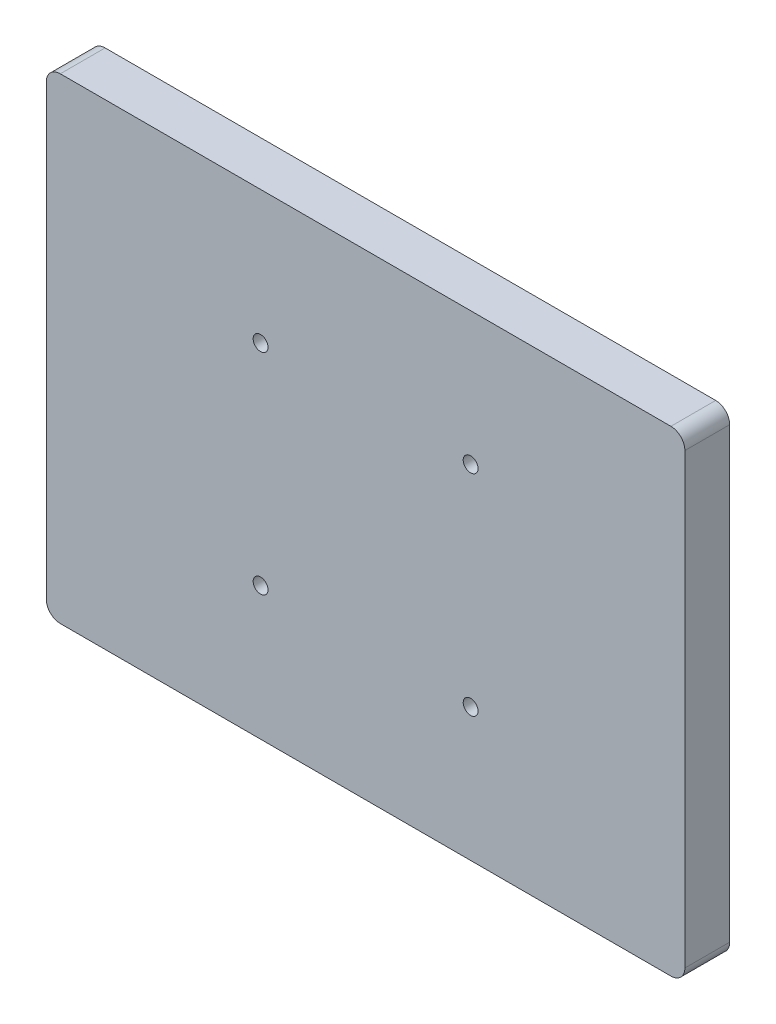
SolidWorks part; units mm, degrees
ref_plane "前视基准面" through (0, 0, 0) normal (0, 0, 1) x (1, 0, 0)
ref_plane "上视基准面" through (0, 0, 0) normal (0, 1, 0) x (1, 0, 0)
ref_plane "右视基准面" through (0, 0, 0) normal (1, 0, 0) x (0, 0, -1)
other "Configuration Table"
sketch "Sketch1" plane through (0, 0, 0) normal (0, 0, 1) x (1, 0, 0)
  line L1 (0, 0) -> (228, 0)
  line L2 (0, 0) -> (0, 170)
  line L3 (0, 170) -> (228, 170)
  line L4 (228, 0) -> (228, 170)
  dimension "D1" = 170
  dimension "D2" = 228
extrude "Boss-Extrude1" add sketch "Sketch1" along normal blind 16
fillet "Fillet1" radius 5 4 edges at (228, 0, 8) (0, 0, 8) (228, 170, 8) (0, 170, 8)
sketch "Sketch2" plane through (0, 0, 16) normal (0, 0, 1) x (1, 0, 0)
  line L0 (0, 85) -> (228, 85) construction
  line L1 (0, 165) -> (0, 5) construction
  line L2 (228, 5) -> (228, 165) construction
  line L3 (114, 170) -> (114, 0) construction
  line L4 (223, 170) -> (5, 170) construction
  line L5 (5, 0) -> (223, 0) construction
  circle A0 centre (76.5, 122.5) radius 2.65
  circle A1 centre (151.5, 122.5) radius 2.65
  circle A2 centre (76.5, 47.5) radius 2.65
  circle A3 centre (151.5, 47.5) radius 2.65
  dimension "D1" = 5.3
  dimension "D2" = 75
  dimension "D3" = 75
extrude "Cut-Extrude1" cut sketch "Sketch2" against normal up to next
